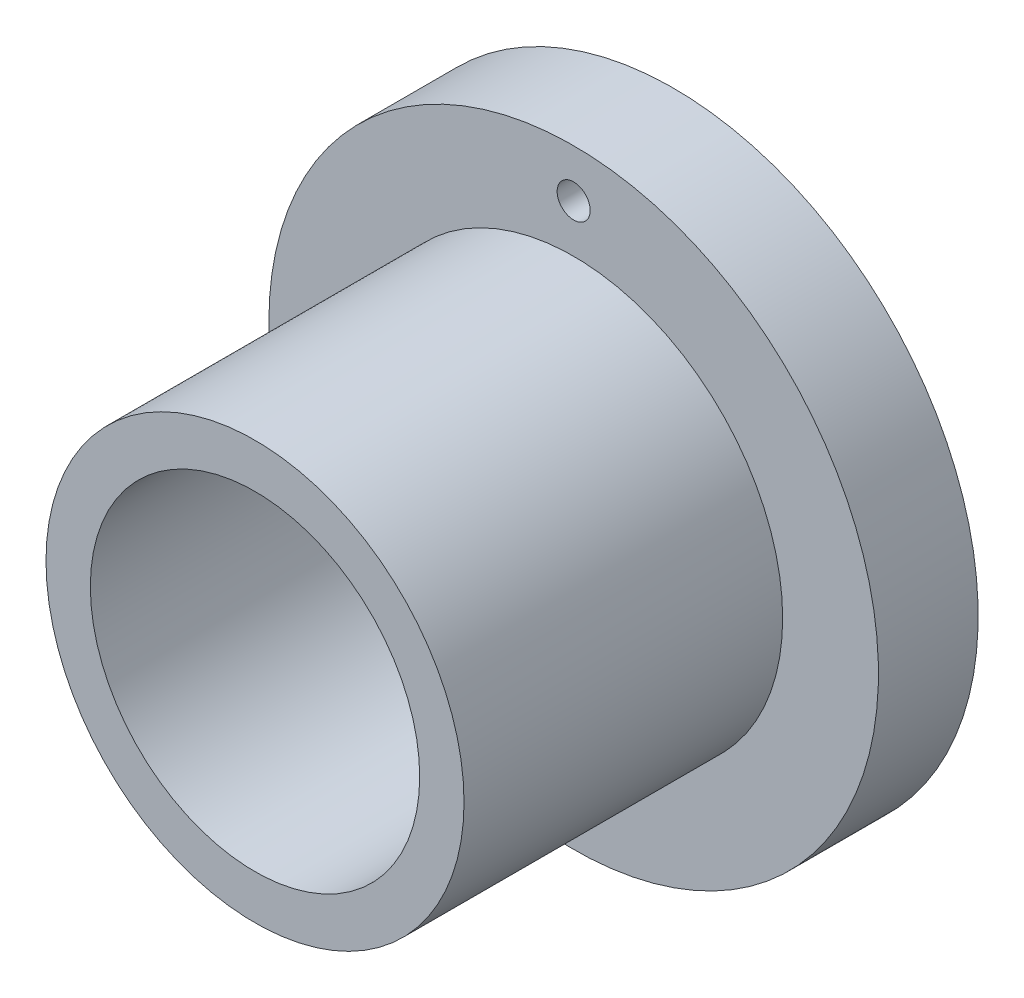
SolidWorks part; units mm, degrees
material "6061-T6 (SS)"
ref_plane "Front Plane" through (0, 0, 0) normal (0, 0, 1) x (1, 0, 0)
ref_plane "Top Plane" through (0, 0, 0) normal (0, 1, 0) x (1, 0, 0)
ref_plane "Right Plane" through (0, 0, 0) normal (1, 0, 0) x (0, 0, -1)
sketch "Sketch1" plane through (0, 0, 0) normal (1, 0, 0) x (0, 0, -1)
  line L0 (0, 0) -> (-29.2608, 0) construction
  line L1 (0, 0) -> (0, -23.1104) construction
  line L2 (0, 5.9436) -> (0, 11) construction
  line L3 (0, 11) -> (15.1, 11) construction
  line L4 (15.1, 11) -> (15.1, 7.5436)
  line L5 (15.1, 7.5436) -> (13, 7.5436)
  line L6 (13, 7.5436) -> (13, 5.9436)
  line L7 (13, 5.9436) -> (0, 5.9436)
  line L8 (0, 7.5436) -> (11.5, 7.5436)
  line L9 (11.5, 7.5436) -> (11.5, 11)
  line L10 (11.5, 11) -> (15.1, 11)
  line L11 (0, 7.5436) -> (0, 5.9436)
  dimension "D1" = 11.8872
  dimension "D2" = 13
  dimension "D3" = 1.6
  dimension "D4" = 2.1
  dimension "D5" = 11
  dimension "D6" = 1.5
revolve "Revolve1" add sketch "Sketch1" angle 360 about L0
sketch "Sketch2" plane through (0, 0, -15.1) normal (0, 0, -1) x (-1, 0, 0)
  line L0 (0, 7.5436) -> (0, 11) construction
  circle A0 centre (0, 0) radius 7.5436 construction
  circle A1 centre (0, 0) radius 11 construction
  point P7 (0, 9.2718)
hole_wizard "#0-80 Tapped Hole1" positions "Sketch4" profile "Sketch3" tap size "#0-80" standard "Ansi Inch" end condition through all
sketch "Sketch4" plane through (0, 0, -15.1) normal (0, 0, -1) x (-1, 0, 0)
  point P0 (0, 9.2718)
cosmetic thread "Hole Thread1" parameters "D2"=1.524
sketch "Sketch3" plane through (0, 9.2718, -15.1) normal (1, 0, 0) x (0, 1, 0)
  line L0 (0, 0) -> (0, 15.1)
  line L1 (0, 15.1) -> (0.5956, 15.1)
  line L2 (0.5956, 15.1) -> (0.5956, 0)
  line L5 (0.5956, 0) -> (0, 0)
  line L11 (0, -6.35) -> (0, 107.95) construction
  dimension "Thru Tap Drill Dia." = 1.1913
  dimension "Thru Tap Drill Depth" = 15.1
mirror "Mirror1" about plane through (0, 0, 0) normal (0, 1, 0) of "#0-80 Tapped Hole1"
